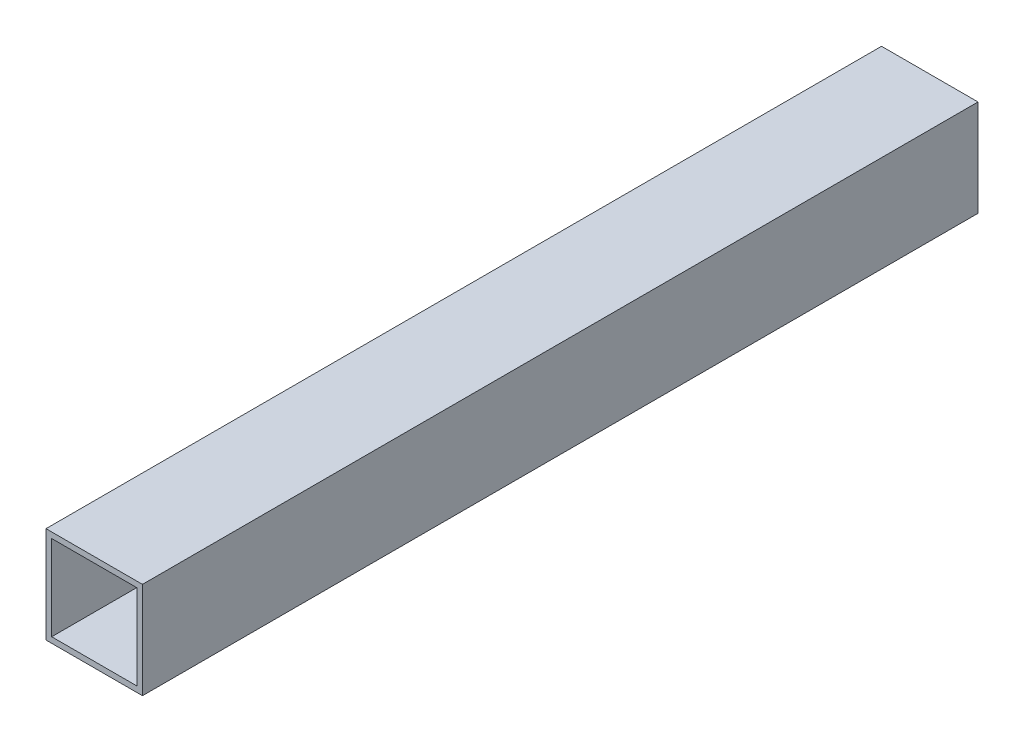
SolidWorks part; units mm, degrees
ref_plane "Front Plane" through (0, 0, 0) normal (0, 0, 1) x (1, 0, 0)
ref_plane "Top Plane" through (0, 0, 0) normal (0, 1, 0) x (1, 0, 0)
ref_plane "Right Plane" through (0, 0, 0) normal (1, 0, 0) x (0, 0, -1)
sketch "Sketch1" plane through (0, 0, 0) normal (0, 0, 1) x (1, 0, 0)
  line L1 (-12.7, -12.7) -> (12.7, -12.7)
  line L2 (-12.7, -12.7) -> (-12.7, 12.7)
  line L3 (-12.7, 12.7) -> (12.7, 12.7)
  line L4 (12.7, -12.7) -> (12.7, 12.7)
  line L5 (-12.7, -12.7) -> (12.7, 12.7) construction
  line L6 (-12.7, 12.7) -> (12.7, -12.7) construction
  line L7 (-11.2, -11.2) -> (11.2, -11.2)
  line L8 (-11.2, -11.2) -> (-11.2, 11.2)
  line L9 (-11.2, 11.2) -> (11.2, 11.2)
  line L10 (11.2, -11.2) -> (11.2, 11.2)
  line L11 (-11.2, -11.2) -> (11.2, 11.2) construction
  line L12 (-11.2, 11.2) -> (11.2, -11.2) construction
  point P0 (0, 0)
  point P6 (0, 0)
  dimension "D1" = 25.4
  dimension "D2" = 25.4
  dimension "D3" = 1.5
extrude "Boss-Extrude1" add sketch "Sketch1" along normal blind 220
